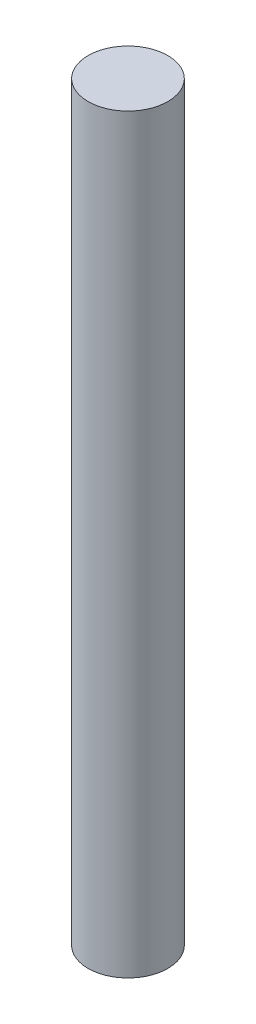
SolidWorks part; units mm, degrees
material "1060 Alloy"
ref_plane "Front Plane" through (0, 0, 0) normal (0, 0, 1) x (1, 0, 0)
ref_plane "Top Plane" through (0, 0, 0) normal (0, 1, 0) x (1, 0, 0)
ref_plane "Right Plane" through (0, 0, 0) normal (1, 0, 0) x (0, 0, -1)
sketch "Sketch1" plane through (0, 0, 0) normal (0, 1, 0) x (1, 0, 0)
  line L0 (0, 0.75) -> (0, -0.75) construction
  circle A0 centre (0, 0) radius 0.75
  dimension "D1" = 1.5
extrude "Boss-Extrude1" add sketch "Sketch1" along normal blind 14.125
